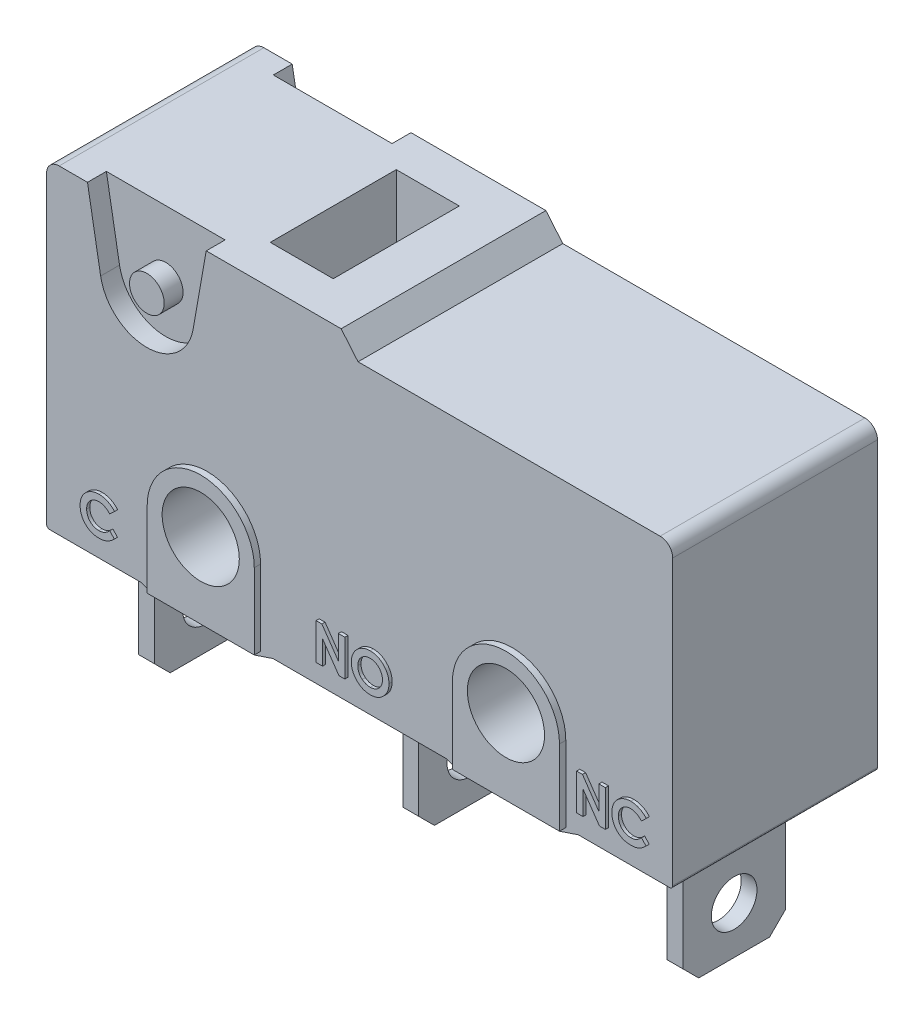
SolidWorks part; units mm, degrees
ref_plane "Front Plane" through (0, 0, 0) normal (0, 0, 1) x (1, 0, 0)
ref_plane "Top Plane" through (0, 0, 0) normal (0, 1, 0) x (1, 0, 0)
ref_plane "Right Plane" through (0, 0, 0) normal (1, 0, 0) x (0, 0, -1)
sketch "Sketch1" plane through (0, 0, 0) normal (0, 0, 1) x (1, 0, 0)
  line L0 (9.353, 0) -> (9.89, -0.64)
  line L1 (0.4, 0) -> (9.353, 0)
  line L2 (0, -0.4) -> (0, -10.15)
  line L3 (0, -10.15) -> (3, -10.15)
  line L4 (19.88, -1.04) -> (19.88, -10.15)
  line L5 (9.89, -0.64) -> (19.48, -0.64)
  line L6 (3, -10.15) -> (3.595, -10.35)
  line L7 (3.595, -10.35) -> (6.595, -10.35)
  line L8 (6.595, -10.35) -> (7.19, -10.15)
  line L9 (12.69, -10.15) -> (13.285, -10.35)
  line L10 (13.285, -10.35) -> (16.285, -10.35)
  line L11 (16.285, -10.35) -> (16.88, -10.15)
  line L12 (7.19, -10.15) -> (12.69, -10.15)
  line L13 (16.88, -10.15) -> (19.88, -10.15)
  arc A0 (0.4, 0) -> (0, -0.4) centre (0.4, -0.4) ccw
  arc A1 (19.48, -0.64) -> (19.88, -1.04) centre (19.48, -1.04) cw
  point P10 (0, 0)
  dimension "D1" = 0.4
  dimension "D2" = 10.15
  dimension "D3" = 9.51
  dimension "D4" = 9.89
  dimension "D5" = 130
  dimension "D6" = 19.88
  dimension "D7" = 3
  dimension "D8" = 3
  dimension "D9" = 3
  dimension "D10" = 5.5
  dimension "D11" = 0.2
extrude "Boss-Extrude1" add sketch "Sketch1" along normal blind 6.5
sketch "Sketch3" plane through (0, 0, 6.5) normal (0, 0, 1) x (1, 0, 0)
  line L0 (3.395, -7.75) -> (3.395, -10.15)
  line L1 (3.395, -10.15) -> (6.795, -10.15)
  line L2 (6.795, -10.15) -> (6.795, -7.75)
  line L3 (3.595, -10.35) -> (6.595, -10.35) construction
  line L4 (5.095, -6.05) -> (14.785, -6.05) construction
  line L5 (7.19, -10.15) -> (12.69, -10.15) construction
  line L6 (13.085, -7.75) -> (13.085, -10.15)
  line L7 (13.085, -10.15) -> (16.485, -10.15)
  line L8 (16.485, -10.15) -> (16.485, -7.75)
  line L9 (13.285, -10.35) -> (16.285, -10.35) construction
  arc A0 (3.395, -7.75) -> (6.795, -7.75) centre (5.095, -7.75) cw
  arc A1 (13.085, -7.75) -> (16.485, -7.75) centre (14.785, -7.75) cw
  point P5 (5.095, -10.15)
  point P6 (5.095, -10.35)
  point P18 (14.785, -10.35)
  point P19 (14.785, -10.15)
  dimension "D1" = 3.4
  dimension "D2" = 4.1
extrude "Boss-Extrude2" add sketch "Sketch3" along normal blind 0.2
ref_plane "Plane1" through (0, 0, 3.25) normal (0, 0, 1) x (1, 0, 0)
mirror "Mirror1" about plane through (0, 0, 3.25) normal (0, 0, 1) of "Boss-Extrude2"
sketch "Sketch4" plane through (0, 0, 6.7) normal (0, 0, 1) x (1, 0, 0)
  circle A0 centre (5.095, -7.75) radius 1.225
  circle A1 centre (14.785, -7.75) radius 1.225
  dimension "D1" = 2.45
extrude "Cut-Extrude1" cut sketch "Sketch4" against normal blind 10.2
fillet "Fillet1" radius 0.1 2 edges at (19.88, -10.15, 3.25) (0, -10.15, 3.25)
sketch "Sketch5" plane through (0, 0, 6.5) normal (0, 0, 1) x (1, 0, 0)
  line L0 (1.7177, -2.3688) -> (1.3, 0)
  line L1 (9.353, 0) -> (0.4, 0) construction
  line L2 (4.6523, -2.3688) -> (5.07, 0)
  line L3 (3.185, -3.6) -> (0, -3.6) construction
  line L4 (0, -0.4) -> (0, -10.05) construction
  line L5 (1.3, 0) -> (5.07, 0)
  arc A0 (1.7177, -2.3688) -> (4.6523, -2.3688) centre (3.185, -2.11) ccw
  circle A1 centre (3.185, -2.11) radius 0.55
  dimension "D5" = 1.1
  dimension "D1" = 3.6
  dimension "D2" = 1.3
  dimension "D3" = 3.77
  dimension "D4" = 100
extrude "Cut-Extrude2" cut sketch "Sketch5" against normal blind 0.6
mirror "Mirror2" about plane through (0, 0, 3.25) normal (0, 0, 1) of "Cut-Extrude2"
sketch "Sketch6" plane through (0, 0, 0) normal (0, 1, 0) x (1, 0, 0)
  line L0 (9.353, -6.5) -> (9.353, 0) construction
  line L1 (5.853, -1.25) -> (7.853, -1.25)
  line L2 (5.853, -1.25) -> (5.853, -5.25)
  line L3 (5.853, -5.25) -> (7.853, -5.25)
  line L4 (7.853, -1.25) -> (7.853, -5.25)
  point P4 (9.353, -3.25)
  point P5 (7.853, -3.25)
  dimension "D1" = 2
  dimension "D2" = 4
  dimension "D3" = 1.5
extrude "Cut-Extrude3" cut sketch "Sketch6" against normal blind 2
sketch "Sketch7" plane through (0, -10.15, 0) normal (0, -1, 0) x (1, 0, 0)
  line L0 (0.1, 6.5) -> (3, 6.5) construction
  line L1 (1.3, 4.875) -> (1.8, 4.875)
  line L2 (1.3, 4.875) -> (1.3, 1.625)
  line L3 (1.3, 1.625) -> (1.8, 1.625)
  line L4 (1.8, 4.875) -> (1.8, 1.625)
  line L5 (9.69, 4.875) -> (10.19, 4.875)
  line L6 (9.69, 4.875) -> (9.69, 1.625)
  line L7 (9.69, 1.625) -> (10.19, 1.625)
  line L8 (10.19, 4.875) -> (10.19, 1.625)
  line L9 (18.08, 4.875) -> (18.58, 4.875)
  line L10 (18.08, 4.875) -> (18.08, 1.625)
  line L11 (18.08, 1.625) -> (18.58, 1.625)
  line L12 (18.58, 4.875) -> (18.58, 1.625)
  line L13 (7.19, 6.5) -> (12.69, 6.5) construction
  line L14 (16.88, 6.5) -> (19.78, 6.5) construction
  line L15 (3, 6.5) -> (3, 0) construction
  point P12 (1.55, 6.5)
  point P13 (1.55, 4.875)
  point P16 (9.94, 4.875)
  point P17 (9.94, 6.5)
  point P18 (18.33, 4.875)
  point P21 (18.33, 6.5)
  point P22 (3, 3.25)
  point P25 (1.8, 3.25)
  point P28 (9.69, 3.25)
  point P29 (18.08, 3.25)
  dimension "D1" = 3.25
  dimension "D2" = 0.5
extrude "Boss-Extrude3" add sketch "Sketch7" along normal blind 4.15
chamfer "Chamfer1" distance 0.5 angle 45 6 edges at (1.55, -14.3, 4.875) (9.94, -14.3, 4.875) (18.33, -14.3, 4.875) (18.33, -14.3, 1.625) (9.94, -14.3, 1.625) (1.55, -14.3, 1.625)
sketch "Sketch8" plane through (1.3, 0, 0) normal (-1, 0, 0) x (0, 0, 1)
  line L0 (4.375, -14.3) -> (2.125, -14.3) construction
  circle A0 centre (3.25, -12.8) radius 0.725
  point P2 (3.25, -14.3)
  dimension "D1" = 1.45
  dimension "D2" = 1.5
extrude "Cut-Extrude4" cut sketch "Sketch8" against normal blind 18.15
sketch "Sketch9" plane through (0, 0, 6.5) normal (0, 0, 1) x (1, 0, 0)
  text T0 "C              NO             NC" font "Century Gothic" height 1.15
extrude "Boss-Extrude4" add sketch "Sketch9" along normal blind 0.1
sketch "Sketch11" plane through (0, 0, 0) normal (0, 0, -1) x (-1, 0, 0)
  text T0 "KW       CE" font "Century Gothic" height 1.78
extrude "Boss-Extrude5" add sketch "Sketch11" along normal blind 0.1
sketch "Sketch12" plane through (0, 0, 0) normal (0, 0, -1) x (-1, 0, 0)
  text T0 "5A  125  250V" font "Century Gothic" height 1.3
extrude "Boss-Extrude6" add sketch "Sketch12" along normal blind 0.1
sketch "Sketch13" plane through (0, 0, 0) normal (0, 0, -1) x (-1, 0, 0)
  text T0 "2                  3                  1" font "Century Gothic" height 1.1
extrude "Boss-Extrude7" add sketch "Sketch13" along normal blind 0.1
sketch "Sketch14" plane through (0, 0, 0) normal (0, 0, -1) x (-1, 0, 0)
  line L0 (-18.2761, -7.6793) -> (-18.2761, -5.3079)
  line L1 (-18.2761, -5.3079) -> (-9.8134, -5.3079)
  line L2 (-9.8134, -5.3079) -> (-9.8134, -5.5774)
  line L3 (-9.8134, -7.7817) -> (-9.8134, -6.3917)
  line L4 (-3.5611, -6.0907) -> (-1.3125, -6.0907)
  line L5 (-1.3125, -6.0907) -> (-1.3125, -7.532)
  line L6 (-1.3125, -7.532) -> (-1.3625, -7.532)
  line L7 (-1.3625, -7.532) -> (-1.3625, -6.1407)
  line L8 (-1.3625, -6.1407) -> (-3.5611, -6.1407)
  line L9 (-3.5611, -6.1407) -> (-3.5611, -6.0907)
  line L10 (-18.2761, -7.6793) -> (-18.2261, -7.6793)
  line L11 (-18.2261, -7.6793) -> (-18.2261, -5.3579)
  line L12 (-18.2261, -5.3579) -> (-9.8634, -5.3579)
  line L13 (-9.8634, -5.3579) -> (-9.8634, -5.5774)
  line L14 (-9.8634, -5.5774) -> (-10.0384, -5.5774)
  line L15 (-10.0384, -5.5774) -> (-9.8384, -5.7774)
  line L16 (-9.8384, -5.7774) -> (-9.6384, -5.5774)
  line L17 (-9.6384, -5.5774) -> (-9.8134, -5.5774)
  line L18 (-9.8134, -7.7817) -> (-9.8634, -7.7817)
  line L19 (-9.8634, -7.7817) -> (-9.8634, -6.3917)
  line L20 (-9.8634, -6.3917) -> (-10.0384, -6.3917)
  line L21 (-10.0384, -6.3917) -> (-9.8384, -6.1917)
  line L22 (-9.8384, -6.1917) -> (-9.6384, -6.3917)
  line L23 (-9.6384, -6.3917) -> (-9.8134, -6.3917)
  line L24 (-9.8634, -5.3079) -> (-9.8634, -5.3579) construction
  line L25 (-9.8634, -5.3579) -> (-9.8134, -5.3579) construction
  line L26 (-9.8384, -6.0124) -> (-8.7652, -6.1417)
  line L27 (-8.7652, -6.1417) -> (-7.7787, -6.1417)
  line L28 (-7.7787, -6.1417) -> (-7.7787, -6.1917)
  line L29 (-7.7787, -6.1917) -> (-8.7652, -6.1917)
  line L30 (-8.7652, -6.1917) -> (-9.8384, -6.0624)
  line L31 (-9.8384, -6.0624) -> (-9.8384, -6.0124)
  line L32 (-9.8634, -5.5774) -> (-9.8134, -5.5774) construction
  point P28 (-9.8384, -5.5774)
  dimension "D1" = 0.05
  dimension "D2" = 0.05
  dimension "D3" = 0.2
  dimension "D4" = 0.2
extrude "Boss-Extrude8" add sketch "Sketch14" along normal blind 0.1
sketch "Sketch15" plane through (0, 0, 0) normal (0, 0, -1) x (-1, 0, 0)
  line L0 (-5.9919, -3.9223) -> (-5.0693, -3.2965) construction
  line L1 (-5.0693, -3.2965) -> (-5.0693, -4.5481) construction
  line L2 (-5.0693, -4.5481) -> (-4.1468, -3.9223) construction
  line L4 (-5.9919, -4.0227) -> (-5.0693, -3.3969) construction
  line L5 (-5.0693, -3.3969) -> (-5.0693, -4.6486) construction
  line L6 (-5.0693, -4.6486) -> (-4.1468, -4.0227) construction
  line L7 (-4.1468, -3.9223) -> (-4.1468, -4.0227)
  line L8 (-5.9919, -3.9223) -> (-5.9919, -4.0227)
  spline S0 degree 3 poles (-5.9919, -3.9223) (-5.0693, -3.2965) (-5.0693, -4.5481) (-4.1468, -3.9223) knots 0 0 0 0 1 1 1 1
  spline S1 degree 3 poles (-5.9919, -4.0227) (-5.0693, -3.3969) (-5.0693, -4.6486) (-4.1468, -4.0227) knots 0 0 0 0 1 1 1 1
  dimension "D1" = 0.1004
extrude "Boss-Extrude9" add sketch "Sketch15" along normal blind 0.1
